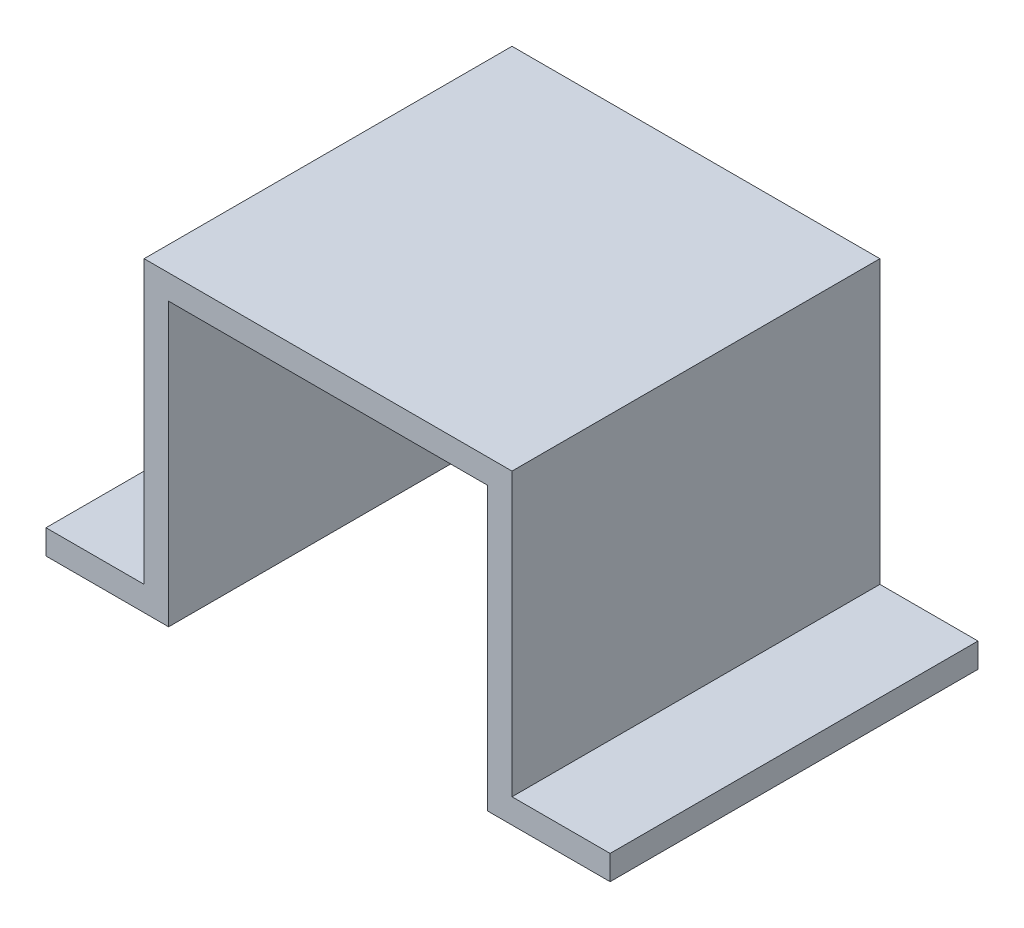
SolidWorks part; units mm, degrees
ref_plane "Front Plane" through (0, 0, 0) normal (0, 0, 1) x (1, 0, 0)
ref_plane "Top Plane" through (0, 0, 0) normal (0, 1, 0) x (1, 0, 0)
ref_plane "Right Plane" through (0, 0, 0) normal (1, 0, 0) x (0, 0, -1)
sketch "Sketch1" plane through (0, 0, 0) normal (0, 0, 1) x (1, 0, 0)
  line L0 (0, 0) -> (10, 0)
  line L1 (10, 0) -> (10, 23)
  line L2 (10, 23) -> (36, 23)
  line L3 (23, -976.7579) -> (23, 49023.2421) construction
  line L4 (36, 0) -> (36, 23)
  line L5 (46, 0) -> (36, 0)
  line L6 (0, 2) -> (8, 2)
  line L7 (8, 2) -> (8, 25)
  line L8 (8, 25) -> (38, 25)
  line L9 (38, 2) -> (38, 25)
  line L10 (46, 2) -> (38, 2)
  line L11 (0, 0) -> (0, 2)
  line L12 (46, 0) -> (46, 2)
  point P8 (23, 23)
  dimension "D2" = 30
  dimension "D3" = 10
  dimension "D4" = 25
  dimension "D1" = 2
extrude "Boss-Extrude1" add sketch "Sketch1" against normal mid plane 30
